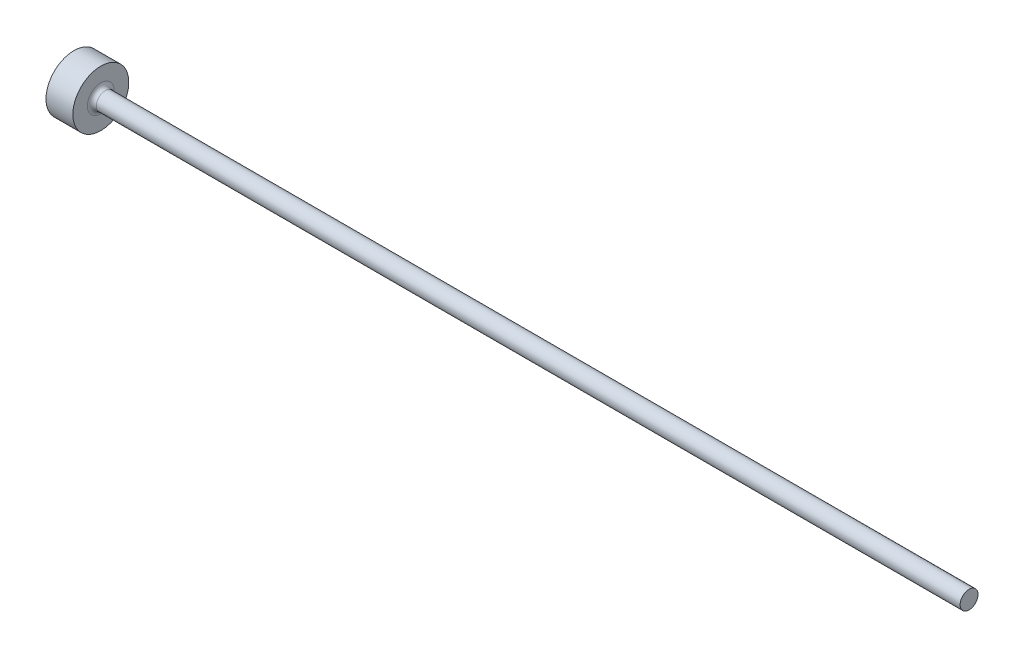
SolidWorks part; units mm, degrees
material "1.2516 "
ref_plane "Ebene vorne" through (0, 0, 0) normal (0, 0, 1) x (1, 0, 0)
ref_plane "Ebene oben" through (0, 0, 0) normal (0, 1, 0) x (1, 0, 0)
ref_plane "Ebene rechts" through (0, 0, 0) normal (1, 0, 0) x (0, 0, -1)
sketch "Skizze1" plane through (0, 0, 0) normal (0, 0, 1) x (1, 0, 0)
  line L0 (0, 0) -> (45, 0) construction
  line L1 (0, 0) -> (0, 1.25)
  line L2 (0, 1.25) -> (1.2, 1.25)
  line L3 (1.2, 1.25) -> (1.2, 0.6)
  line L4 (1.4, 0.4) -> (40, 0.4)
  line L5 (40, 0.4) -> (40, 0)
  line L6 (40, 0) -> (0, 0)
  arc A0 (1.2, 0.6) -> (1.4, 0.4) centre (1.4, 0.6) ccw
  dimension "Radius" = 0.2
  dimension "Durchmesser1" = 0.8
  dimension "Durchmesser2" = 2.5
  dimension "Länge" = 40
  dimension "Kopflänge" = 1.2
  dimension "D6" = 5
revolve "Rotation1" add sketch "Skizze1" angle 360 about L0
other "PropertyManager"
